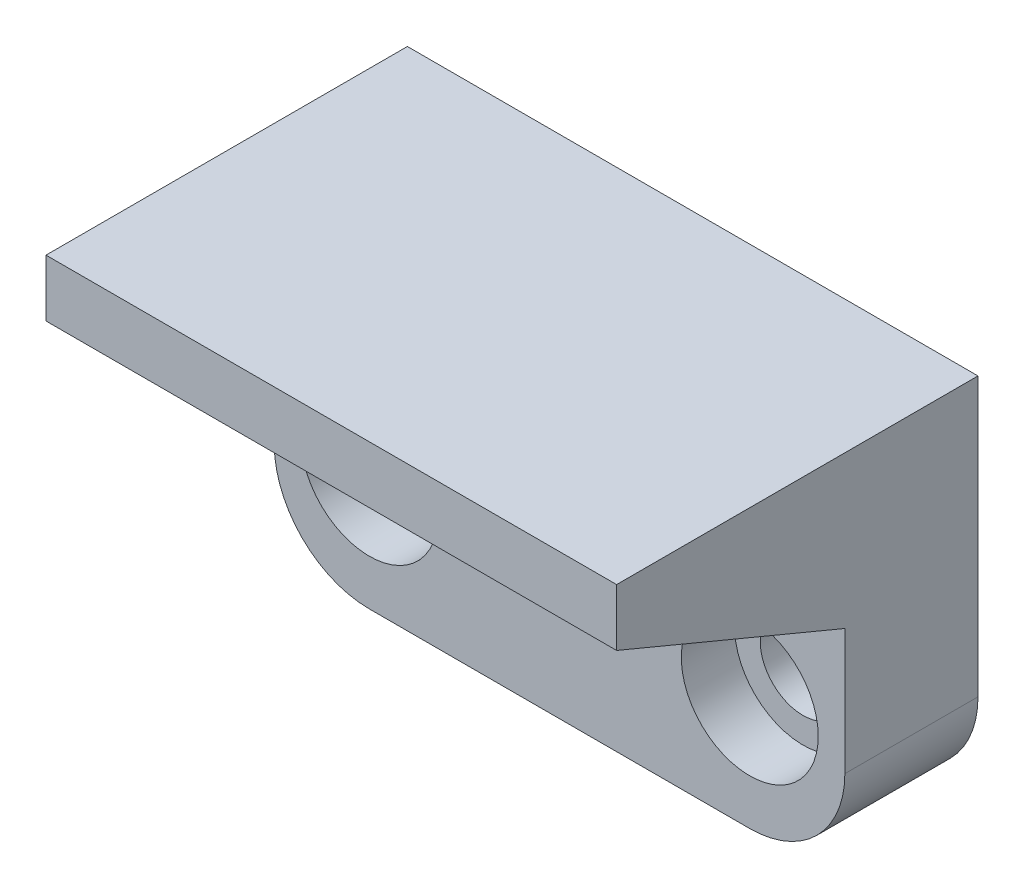
SolidWorks part; units mm, degrees
ref_plane "Front Plane" through (0, 0, 0) normal (0, 0, 1) x (1, 0, 0)
ref_plane "Top Plane" through (0, 0, 0) normal (0, 1, 0) x (1, 0, 0)
ref_plane "Right Plane" through (0, 0, 0) normal (1, 0, 0) x (0, 0, -1)
sketch "Sketch1" plane through (0, 0, 0) normal (0, 0, 1) x (1, 0, 0)
  line L1 (-15, 9.805) -> (15, 9.805)
  line L2 (-15, 9.805) -> (-15, -9.805)
  line L3 (-15, -9.805) -> (15, -9.805)
  line L4 (15, 9.805) -> (15, -9.805)
  line L5 (-15, 9.805) -> (15, -9.805) construction
  line L6 (-15, -9.805) -> (15, 9.805) construction
  circle A0 centre (-10, -3.805) radius 2.25
  circle A1 centre (10, -3.805) radius 2.25
  point P0 (0, 0)
  dimension "D3" = 13.61
  dimension "D4" = 13.61
  dimension "D5" = 20
  dimension "D6" = 5
  dimension "D7" = 4.5
  dimension "D8" = 4.5
  dimension "D1" = 19.61
  dimension "D2" = 30
extrude "Boss-Extrude1" add sketch "Sketch1" along normal blind 7
sketch "Sketch2" plane through (0, 0, 7) normal (0, 0, 1) x (1, 0, 0)
  circle A0 centre (-10, -3.805) radius 3.6
  circle A1 centre (10, -3.805) radius 3.6
  dimension "D1" = 7.2
  dimension "D2" = 7.2
extrude "Cut-Extrude1" cut sketch "Sketch2" against normal blind 2.8
fillet "Fillet2" radius 5 2 edges at (15, -9.805, 3.5) (-15, -9.805, 3.5)
sketch "Sketch3" plane through (-15, 0, 0) normal (-1, 0, 0) x (0, 0, 1)
  line L2 (7, 9.805) -> (7, -4.805) construction
  line L3 (7, 1.805) -> (7, 9.805)
  line L4 (7, 9.805) -> (19, 9.805)
  line L5 (19, 9.805) -> (19, 6.805)
  line L6 (19, 6.805) -> (7, 1.805)
  dimension "D1" = 8
  dimension "D2" = 12
  dimension "D3" = 3
  dimension "D4" = 13
extrude "Boss-Extrude2" add sketch "Sketch3" against normal through all
sketch "Sketch4" plane through (-15, 0, 0) normal (-1, 0, 0) x (0, 0, 1)
  line L0 (-1.7, 9.805) -> (-4.2, 9.805)
  line L1 (0, 9.805) -> (-1.7, 9.805)
  line L2 (0, 9.805) -> (0, 6.805)
  line L3 (0, 6.805) -> (-1.7, 6.805)
  line L4 (-1.7, 9.805) -> (-1.7, 6.805)
  line L5 (-4.2, 9.805) -> (-4.2, 5.305)
  line L6 (-4.2, 5.305) -> (-2.7, 5.305)
  line L7 (-2.7, 5.305) -> (-1.7, 6.805)
  line M3 (0, 9.805) -> (0, -4.805)
  dimension "D1" = 1.7
  dimension "D2" = 3
  dimension "D3" = 2.5
  dimension "D4" = 4.5
  dimension "D5" = 1.5
extrude "Boss-Extrude3" [suppressed] add sketch "Sketch4" against normal through all contours L6 L7 L4 L0 L5 | L1 L4 L3 M3
